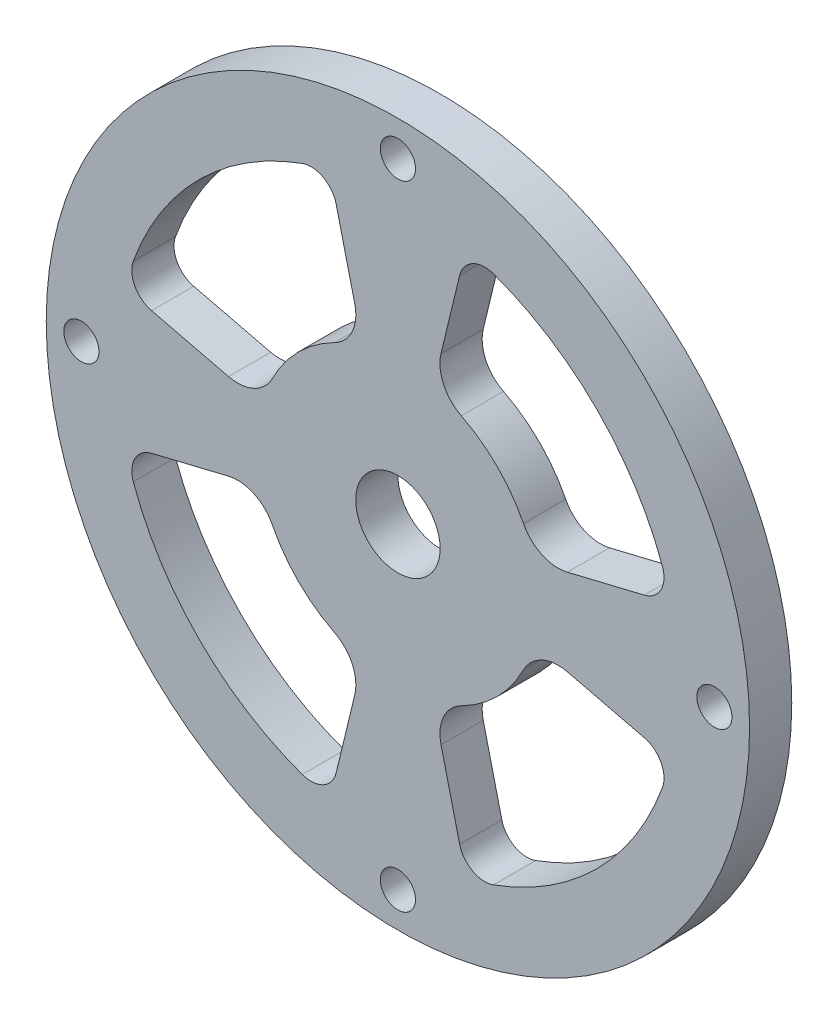
SolidWorks part; units mm, degrees
ref_plane "Front Plane" through (0, 0, 0) normal (0, 0, 1) x (1, 0, 0)
ref_plane "Top Plane" through (0, 0, 0) normal (0, 1, 0) x (1, 0, 0)
ref_plane "Right Plane" through (0, 0, 0) normal (1, 0, 0) x (0, 0, -1)
sketch "Sketch1" plane through (0, 0, 0) normal (0, 0, 1) x (1, 0, 0)
  line L0 (0, 25) -> (0, 0) construction
  line L1 (0, 0) -> (25, 0) construction
  line L2 (4.3904, 17.5128) -> (3.0665, 12.0425)
  line L3 (0, 0) -> (17.6777, 17.6777) construction
  line L4 (17.5128, 4.3904) -> (12.0425, 3.0665)
  line L5 (0.5209, 2.9544) -> (0, 0) construction
  line L6 (4.3904, -17.5128) -> (3.0665, -12.0425)
  line L7 (17.5128, -4.3904) -> (12.0425, -3.0665)
  line L8 (-17.5128, -4.3904) -> (-12.0425, -3.0665)
  line L9 (-4.3904, -17.5128) -> (-3.0665, -12.0425)
  line L10 (-4.3904, 17.5128) -> (-3.0665, 12.0425)
  line L11 (-17.5128, 4.3904) -> (-12.0425, 3.0665)
  line L12 (15.9099, 15.9099) -> (15.9099, 0) construction
  circle A0 centre (0, 0) radius 25
  circle A1 centre (0, 22.5) radius 1.25
  arc A2 (6.8006, 18.8083) -> (18.8083, 6.8006) centre (0, 0) cw
  arc A3 (6.8006, 18.8083) -> (4.3904, 17.5128) centre (6.176, 17.0806) ccw
  circle A4 centre (0, 0) radius 3
  arc A5 (3.0665, 12.0425) -> (4.5063, 8.9271) centre (5.751, 11.3928) ccw
  arc A6 (8.9271, 4.5063) -> (4.5063, 8.9271) centre (0, 0) ccw
  arc A7 (12.0425, 3.0665) -> (8.9271, 4.5063) centre (11.3928, 5.751) cw
  arc A8 (18.8083, 6.8006) -> (17.5128, 4.3904) centre (17.0806, 6.176) cw
  circle A9 centre (22.5, 0) radius 1.25
  circle A10 centre (0, -22.5) radius 1.25
  circle A11 centre (-22.5, 0) radius 1.25
  arc A12 (6.8006, -18.8083) -> (4.3904, -17.5128) centre (6.176, -17.0806) cw
  arc A13 (3.0665, -12.0425) -> (4.5063, -8.9271) centre (5.751, -11.3928) cw
  arc A14 (4.5063, -8.9271) -> (8.9271, -4.5063) centre (0, 0) ccw
  arc A15 (12.0425, -3.0665) -> (8.9271, -4.5063) centre (11.3928, -5.751) ccw
  arc A16 (18.8083, -6.8006) -> (17.5128, -4.3904) centre (17.0806, -6.176) ccw
  arc A17 (18.8083, -6.8006) -> (6.8006, -18.8083) centre (0, 0) cw
  arc A18 (-18.8083, -6.8006) -> (-17.5128, -4.3904) centre (-17.0806, -6.176) cw
  arc A19 (-12.0425, -3.0665) -> (-8.9271, -4.5063) centre (-11.3928, -5.751) cw
  arc A20 (-8.9271, -4.5063) -> (-4.5063, -8.9271) centre (0, 0) ccw
  arc A21 (-3.0665, -12.0425) -> (-4.5063, -8.9271) centre (-5.751, -11.3928) ccw
  arc A22 (-6.8006, -18.8083) -> (-4.3904, -17.5128) centre (-6.176, -17.0806) ccw
  arc A23 (-6.8006, -18.8083) -> (-18.8083, -6.8006) centre (0, 0) cw
  arc A24 (-6.8006, 18.8083) -> (-4.3904, 17.5128) centre (-6.176, 17.0806) cw
  arc A25 (-3.0665, 12.0425) -> (-4.5063, 8.9271) centre (-5.751, 11.3928) cw
  arc A26 (-4.5063, 8.9271) -> (-8.9271, 4.5063) centre (0, 0) ccw
  arc A27 (-12.0425, 3.0665) -> (-8.9271, 4.5063) centre (-11.3928, 5.751) ccw
  arc A28 (-18.8083, 6.8006) -> (-17.5128, 4.3904) centre (-17.0806, 6.176) ccw
  arc A29 (-18.8083, 6.8006) -> (-6.8006, 18.8083) centre (0, 0) cw
  circle A30 centre (0, 0) radius 22.5 construction
  point P31 (0, 0)
  point P67 (0, 0)
  point P69 (0, 0)
  point P71 (0, 0)
  dimension "D2" = 4
  dimension "D3" = 6
  dimension "D5" = 10
  dimension "D8" = 2.5
  dimension "D9" = 5
  dimension "D7" = 45
  dimension "D13" = 50
  dimension "D4" = 4
  dimension "D11" = 45
extrude "Boss-Extrude1" add sketch "Sketch1" along normal blind 3
